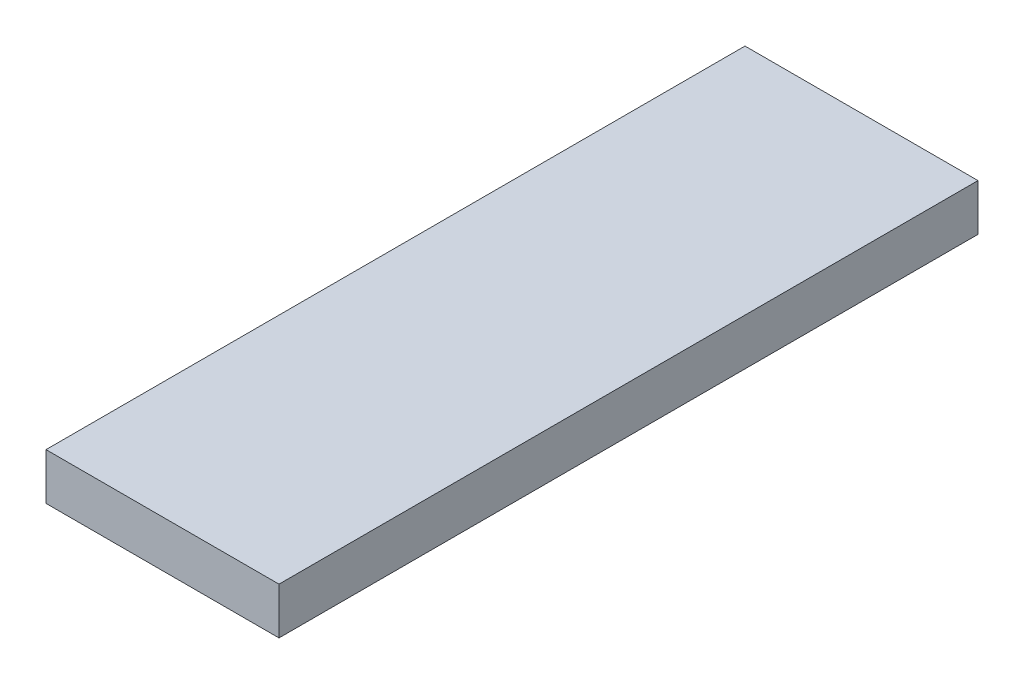
SolidWorks part; units mm, degrees
ref_plane "Front Plane" through (0, 0, 0) normal (0, 0, 1) x (1, 0, 0)
ref_plane "Top Plane" through (0, 0, 0) normal (0, 1, 0) x (1, 0, 0)
ref_plane "Right Plane" through (0, 0, 0) normal (1, 0, 0) x (0, 0, -1)
sketch "Sketch1" plane through (0, 0, 0) normal (0, 0, 1) x (1, 0, 0)
  line L1 (-5, -1) -> (5, -1)
  line L2 (-5, -1) -> (-5, 1)
  line L3 (-5, 1) -> (5, 1)
  line L4 (5, -1) -> (5, 1)
  line L5 (-5, -1) -> (5, 1) construction
  line L6 (-5, 1) -> (5, -1) construction
  point P0 (0, 0)
  dimension "D1" = 10
  dimension "D2" = 2
extrude "Boss-Extrude1" add sketch "Sketch1" along normal blind 30
